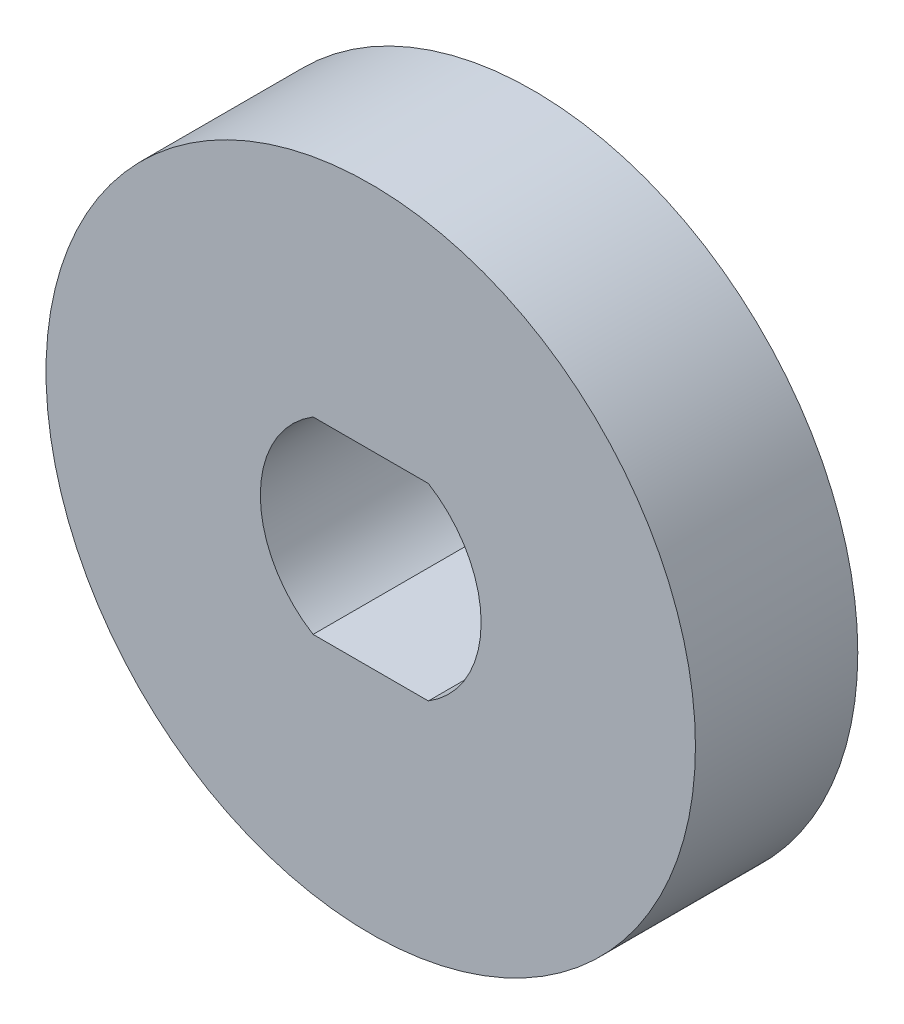
SolidWorks part; units mm, degrees
ref_plane "Front Plane" through (0, 0, 0) normal (0, 0, 1) x (1, 0, 0)
ref_plane "Top Plane" through (0, 0, 0) normal (0, 1, 0) x (1, 0, 0)
ref_plane "Right Plane" through (0, 0, 0) normal (1, 0, 0) x (0, 0, -1)
sketch "Sketch1" plane through (0, 0, 0) normal (0, 0, 1) x (1, 0, 0)
  line L0 (-1.7748, 2.9) -> (1.7748, 2.9)
  line L1 (-1.6583, -2.5) -> (1.6583, -2.5) construction
  line L2 (-1.6583, -2.5) -> (-1.6583, 2.5) construction
  line L3 (-1.6583, 2.5) -> (1.6583, 2.5) construction
  line L4 (1.6583, -2.5) -> (1.6583, 2.5) construction
  line L5 (-1.6583, -2.5) -> (1.6583, 2.5) construction
  line L6 (-1.6583, 2.5) -> (1.6583, -2.5) construction
  line L7 (-1.7748, -2.9) -> (1.7748, -2.9)
  circle A0 centre (0, 0) radius 10
  arc A1 (-1.6583, 2.5) -> (-1.6583, -2.5) centre (0, 0) ccw construction
  arc A2 (1.6583, -2.5) -> (1.6583, 2.5) centre (0, 0) ccw construction
  arc A3 (1.7748, -2.9) -> (1.7748, 2.9) centre (0, 0) ccw
  arc A4 (-1.7748, 2.9) -> (-1.7748, -2.9) centre (0, 0) ccw
  dimension "D1" = 20
  dimension "D2" = 6
  dimension "D3" = 2.5
  dimension "D4" = 0.4
extrude "Boss-Extrude1" add sketch "Sketch1" along normal blind 5
